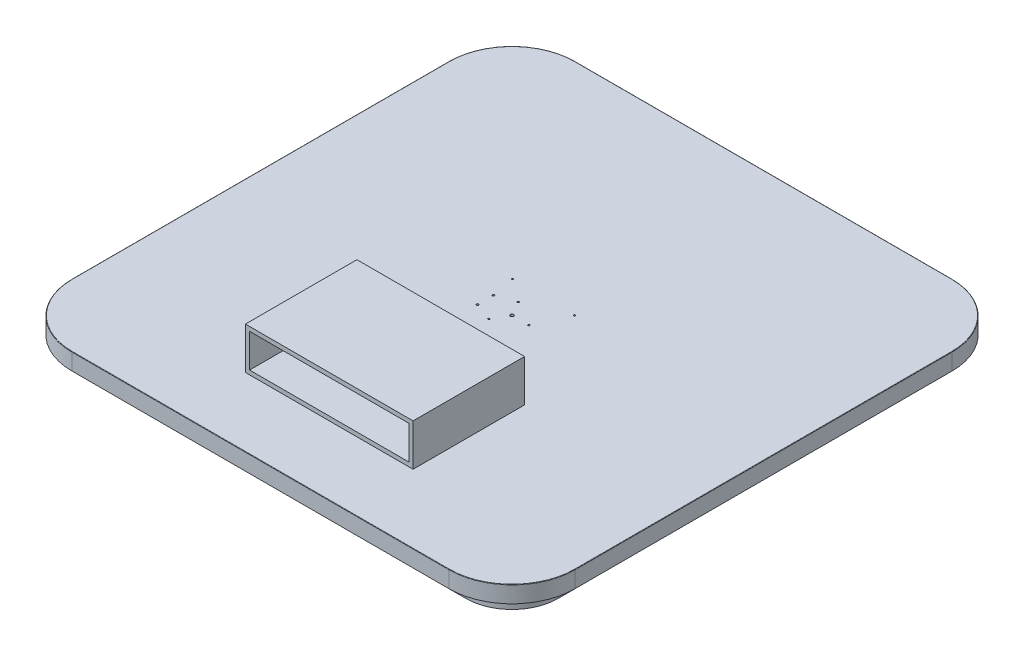
SolidWorks part; units mm, degrees
ref_plane "Front Plane" through (0, 0, 0) normal (0, 0, 1) x (1, 0, 0)
ref_plane "Top Plane" through (0, 0, 0) normal (0, 1, 0) x (1, 0, 0)
ref_plane "Right Plane" through (0, 0, 0) normal (1, 0, 0) x (0, 0, -1)
sketch "Sketch1" plane through (0, 0, 0) normal (0, 1, 0) x (1, 0, 0)
  line L1 (-450, -600) -> (450, -600)
  line L2 (-600, -450) -> (-600, 450)
  line L3 (-450, 600) -> (450, 600)
  line L4 (600, -450) -> (600, 450)
  line L5 (-600, -600) -> (600, 600) construction
  line L6 (-600, 600) -> (600, -600) construction
  arc A0 (450, 600) -> (600, 450) centre (450, 450) cw
  arc A1 (600, -450) -> (450, -600) centre (450, -450) cw
  arc A2 (-450, -600) -> (-600, -450) centre (-450, -450) cw
  arc A3 (-600, 450) -> (-450, 600) centre (-450, 450) cw
  point P0 (0, 0)
  dimension "D3" = 150
  dimension "D1" = 1200
  dimension "D2" = 1200
extrude "Boss-Extrude1" add sketch "Sketch1" along normal blind 40
sketch "Sketch2" plane through (0, 0, 0) normal (0, -1, 0) x (1, 0, 0)
  line L8 (560, -450) -> (560, 450)
  line L9 (450, 560) -> (-450, 560)
  line L10 (-560, 450) -> (-560, -450)
  line L11 (-450, -560) -> (450, -560)
  line L12 (560, -450) -> (560, 450)
  line L13 (450, 560) -> (-450, 560)
  line L14 (-560, 450) -> (-560, -450)
  line L15 (-450, -560) -> (450, -560)
  arc A8 (450, -560) -> (560, -450) centre (450, -450) ccw
  arc A9 (560, 450) -> (450, 560) centre (450, 450) ccw
  arc A10 (-450, 560) -> (-560, 450) centre (-450, 450) ccw
  arc A11 (-560, -450) -> (-450, -560) centre (-450, -450) ccw
  arc A12 (450, -560) -> (560, -450) centre (450, -450) ccw
  arc A13 (560, 450) -> (450, 560) centre (450, 450) ccw
  arc A14 (-450, 560) -> (-560, 450) centre (-450, 450) ccw
  arc A15 (-560, -450) -> (-450, -560) centre (-450, -450) ccw
  dimension "D1" = 40
extrude "Boss-Extrude2" add sketch "Sketch2" along normal blind 40
sketch "Sketch3" plane through (0, -40, 0) normal (0, -1, 0) x (1, 0, 0)
  line L1 (-100, 100) -> (100, 100)
  line L2 (-100, 100) -> (-100, -100)
  line L3 (-100, -100) -> (100, -100)
  line L4 (100, 100) -> (100, -100)
  line L5 (-100, 100) -> (100, -100) construction
  line L6 (-100, -100) -> (100, 100) construction
  point P0 (0, 0)
  dimension "D1" = 200
  dimension "D2" = 200
extrude "Cut-Extrude1" cut sketch "Sketch3" against normal blind 6.35
sketch "Sketch4" plane through (0, -40, 0) normal (0, -1, 0) x (-1, 0, 0)
  circle A0 centre (63.4872, 19.0926) radius 2.4892
  circle A1 centre (63.5128, -19.0074) radius 2.4892
  circle A2 centre (0, 0) radius 3.9687
extrude "Cut-Extrude2" cut sketch "Sketch4" against normal through all
hole_wizard "#10-32 Tapped Hole1" positions "Sketch6" profile "Sketch5" tap size "#10-32" standard "ANSI Inch" end condition through all
sketch "Sketch6" plane through (0, -40, 0) normal (0, -1, 0) x (-1, 0, 0)
  point P0 (20.1378, 34.9338)
  point P3 (-40.3225, -0.027)
  point P6 (20.1846, -34.9068)
cosmetic thread "Hole Thread1" parameters "D2"=4.826
cosmetic thread "Hole Thread2" parameters "D2"=4.826
cosmetic thread "Hole Thread3" parameters "D2"=4.826
sketch "Sketch5" plane through (-20.1378, -40, -34.9338) normal (1, 0, 0) x (0, 0, -1)
  line L0 (0, 0) -> (0, 80)
  line L1 (0, 80) -> (2.0193, 80)
  line L2 (2.0193, 80) -> (2.0193, 0)
  line L5 (2.0193, 0) -> (0, 0)
  line L11 (0, -6.35) -> (0, 107.95) construction
  dimension "Thru Tap Drill Dia." = 4.0386
  dimension "Thru Tap Drill Depth" = 80
sketch "Sketch10" plane through (0, -40, 0) normal (0, -1, 0) x (-1, 0, 0)
  circle A0 centre (-74.65, 74.55) radius 2.02
  circle A1 centre (74.5493, 75.7106) radius 2.02
  circle A2 centre (74.65, -74.55) radius 2.02
  circle A3 centre (-74.55, -74.65) radius 2.032
extrude "Cut-Extrude3" cut sketch "Sketch10" against normal through all
sketch "Sketch11" plane through (0, -40, 0) normal (0, -1, 0) x (-1, 0, 0)
  line L0 (-100, 100) -> (-100, -100) construction
  line L1 (-100, -120) -> (100, -120)
  line L2 (-100, -120) -> (-100, -170)
  line L3 (-100, -170) -> (100, -170)
  line L4 (100, -120) -> (100, -170)
  line L5 (100, -100) -> (100, 100) construction
  line L6 (-100, -100) -> (100, -100) construction
  dimension "D1" = 20
  dimension "D2" = 50
extrude "Cut-Extrude4" cut sketch "Sketch11" against normal through all
fillet "Fillet1" radius 1 8 edges at (556.066, 40, -556.066) (600, 40, 0) (556.066, 40, 556.066) (0, 40, 600) (-556.066, 40, 556.066) (-600, 40, 0) (-556.066, 40, -556.066) (0, 40, -600)
sketch "Sketch12" plane through (0, 40, 0) normal (0, 1, 0) x (1, 0, 0)
  line L0 (100, -120) -> (100, -170) construction
  line L1 (200, -170) -> (-200, -170)
  line L2 (200, -170) -> (200, -436)
  line L3 (200, -436) -> (-200, -436)
  line L4 (-200, -170) -> (-200, -436)
  line L5 (-100, -170) -> (-100, -120) construction
  line L6 (-434.9963, -436) -> (435.0037, -436) construction
  line L8 (100, -170) -> (-100, -170) construction
  dimension "D1" = 100
  dimension "D2" = 100
  dimension "D3" = 0
  dimension "D4" = 0
extrude "Boss-Extrude3" add sketch "Sketch12" along normal blind 100
sketch "Sketch13" plane through (0, 0, 436) normal (0, 0, 1) x (1, 0, 0)
  line L8 (-190, 50) -> (190, 50)
  line L9 (190, 50) -> (190, 130)
  line L10 (190, 130) -> (-190, 130)
  line L11 (-190, 130) -> (-190, 50)
  line L12 (-190, 50) -> (190, 50)
  line L13 (190, 50) -> (190, 130)
  line L14 (190, 130) -> (-190, 130)
  line L15 (-190, 130) -> (-190, 50)
  dimension "D1" = 10
extrude "Cut-Extrude5" cut sketch "Sketch13" against normal up to surface (266 mm away) up to face at (0, 45, 170)
sketch "Sketch14" plane through (0, -40, 0) normal (0, -1, 0) x (-1, 0, 0)
  line L0 (450, -545) -> (-450, -545) construction
  line L1 (-450, -535) -> (-295, -535)
  line L2 (-535, -450) -> (-535, -295)
  line L3 (-535, -295) -> (-295, -295)
  line L4 (-295, -535) -> (-295, -295)
  line L5 (-545, -450) -> (-545, 450) construction
  arc A0 (-450, -535) -> (-535, -450) centre (-450, -450) cw
  dimension "D1" = 85
  dimension "D2" = 10
  dimension "D3" = 10
  dimension "D4" = 240
  dimension "D5" = 240
extrude "Cut-Extrude6" cut sketch "Sketch14" against normal blind 6.35
